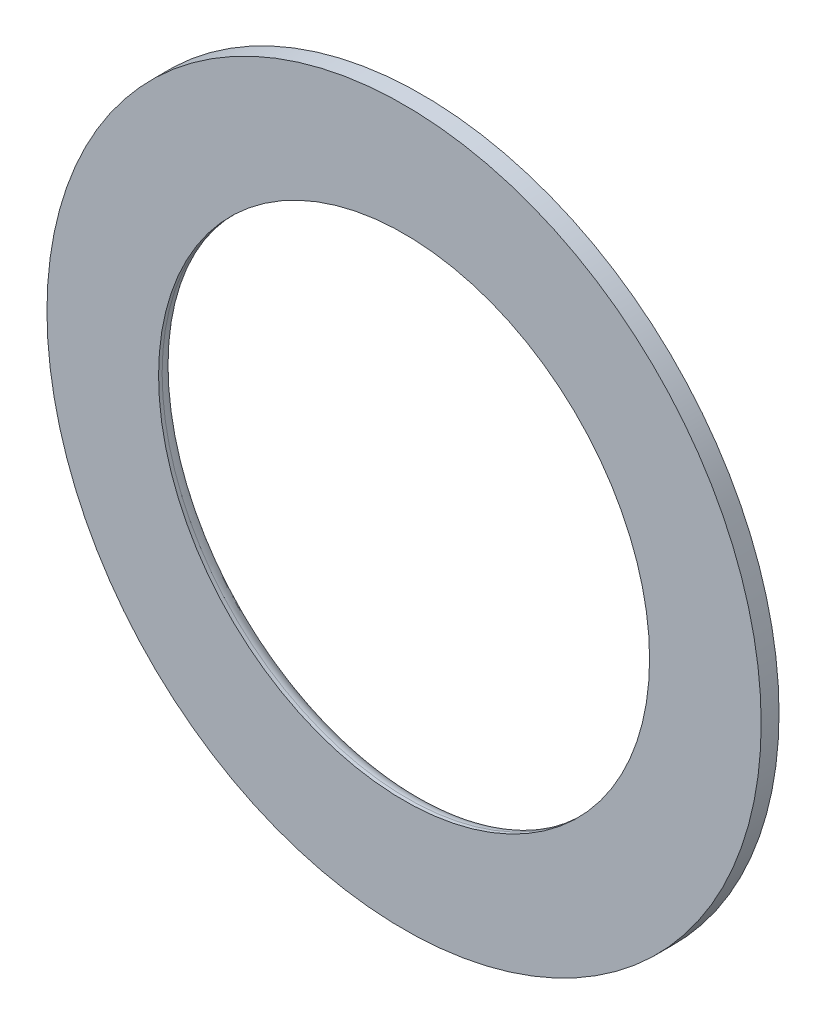
SolidWorks part; units mm, degrees
material "AISI 1010 Steel, hot rolled bar"
ref_plane "Front Plane" through (0, 0, 0) normal (0, 0, 1) x (1, 0, 0)
ref_plane "Top Plane" through (0, 0, 0) normal (0, 1, 0) x (1, 0, 0)
ref_plane "Right Plane" through (0, 0, 0) normal (1, 0, 0) x (0, 0, -1)
sketch "Sketch1" plane through (0, 0, 0) normal (0, 0, 1) x (1, 0, 0)
  circle A0 centre (0, 0) radius 27.5
  circle A1 centre (0, 0) radius 40
  dimension "D1" = 80
  dimension "D2" = 55
extrude "Boss-Extrude1" add sketch "Sketch1" along normal blind 2
fillet "Fillet1" radius 1.6 1 edges at (27.5, 0, 0)
